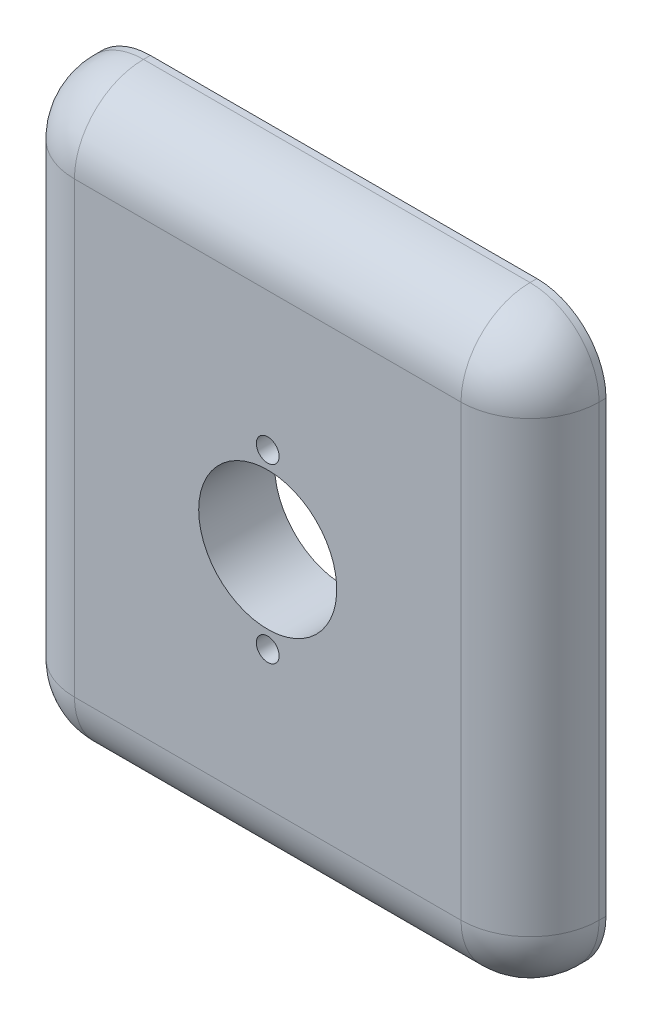
SolidWorks part; units mm, degrees
ref_plane "Alzado" through (0, 0, 0) normal (0, 0, 1) x (1, 0, 0)
ref_plane "Planta" through (0, 0, 0) normal (0, 1, 0) x (1, 0, 0)
ref_plane "Vista lateral" through (0, 0, 0) normal (1, 0, 0) x (0, 0, -1)
sketch "Croquis1" plane through (0, 0, 0) normal (0, 0, 1) x (1, 0, 0)
  line L1 (38, 42.5) -> (-38, 42.5)
  line L2 (38, 42.5) -> (38, -42.5)
  line L3 (38, -42.5) -> (-38, -42.5)
  line L4 (-38, 42.5) -> (-38, -42.5)
  line L5 (38, 42.5) -> (-38, -42.5) construction
  line L6 (38, -42.5) -> (-38, 42.5) construction
  point P0 (0, 0)
  dimension "D1" = 76
  dimension "D2" = 85
extrude "Saliente-Extruir1" add sketch "Croquis1" along normal blind 11
sketch "Croquis3" plane through (0, 0, 0) normal (0, 0, -1) x (-1, 0, 0)
  line L0 (0, -30) -> (0, 30) construction
  line L1 (-30, -30) -> (30, -30)
  line L4 (30, -30) -> (30, 30)
  line L5 (-30, -30) -> (30, 30) construction
  line L6 (-30, 30) -> (30, -30) construction
  line L7 (30, 0) -> (-30, 0) construction
  circle A0 centre (28, -28) radius 1.65
  circle A1 centre (-28, -28) radius 1.65
  circle A2 centre (-28, 28) radius 1.65
  circle A3 centre (28, 28) radius 1.65
  point P0 (0, 0)
  dimension "D3" = 3.3
  dimension "D1" = 60
  dimension "D2" = 60
  dimension "D4" = 2
  dimension "D5" = 2
extrude "Cortar-Extruir2" cut sketch "Croquis3" against normal blind 5 contours A0 | A1 | A2 | A3
sketch "Croquis4" plane through (0, 0, 0) normal (0, 0, -1) x (-1, 0, 0)
  circle A0 centre (28, 28) radius 3
  circle A1 centre (28, -28) radius 3
  circle A2 centre (-28, 28) radius 3
  circle A3 centre (-28, -28) radius 3
  dimension "D1" = 6
  dimension "D2" = 6
  dimension "D3" = 6
  dimension "D4" = 6
extrude "Cortar-Extruir3" cut sketch "Croquis4" against normal blind 2
fillet "Redondeo3" radius 10 8 edges at (0, -42.5, 11) (38, 0, 11) (0, 42.5, 11) (-38, 0, 11) (-38, -42.5, 5.5) (38, -42.5, 5.5) (38, 42.5, 5.5) (-38, 42.5, 5.5)
sketch "Croquis5" plane through (0, 0, 0) normal (0, 0, -1) x (-1, 0, 0)
  line L0 (0, 0) -> (0, 12.5) construction
  line L1 (-10, 0) -> (10, 0) construction
  circle A0 centre (0, 0) radius 10
  circle A1 centre (0, 12.5) radius 1.65
  circle A2 centre (0, -12.5) radius 1.65
  dimension "D1" = 20
  dimension "D3" = 3.3
  dimension "D2" = 12.5
extrude "Cortar-Extruir4" cut sketch "Croquis5" against normal through all
